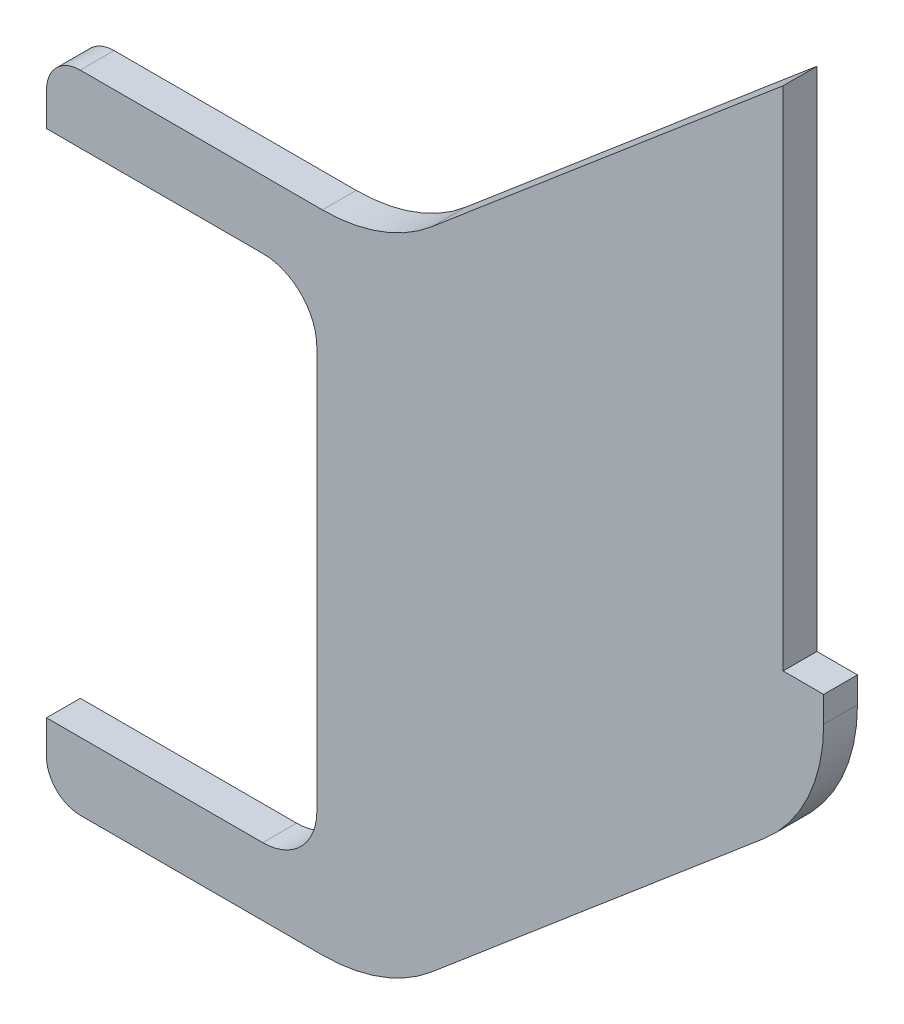
SolidWorks part; units mm, degrees
material "Acier allié"
ref_plane "Plan de face" through (0, 0, 0) normal (0, 0, 1) x (1, 0, 0)
ref_plane "Plan de dessus" through (0, 0, 0) normal (0, 1, 0) x (1, 0, 0)
ref_plane "Plan de droite" through (0, 0, 0) normal (1, 0, 0) x (0, 0, -1)
sketch "Esquisse1" plane through (0, 0, 0) normal (0, 0, 1) x (1, 0, 0)
  line L0 (80, 171) -> (0, 171)
  line L1 (0, 0) -> (100, 0)
  line L2 (0, 191) -> (100, 191)
  line L3 (100, 191) -> (218, 291)
  line L4 (0, 171) -> (0, 191)
  line L5 (80, 20) -> (0, 20)
  line L6 (80, 20) -> (80, 171)
  line L7 (0, 20) -> (0, 0)
  line L8 (230, 110.1695) -> (230, 141)
  line L9 (230, 110.1695) -> (100, 0)
  line L10 (230, 141) -> (218, 141)
  line L11 (218, 141) -> (218, 291)
  dimension "D1" = 151
  dimension "D2" = 80
  dimension "D3" = 80
  dimension "D4" = 20
  dimension "D5" = 20
  dimension "D6" = 100
  dimension "D7" = 150
  dimension "D8" = 100
  dimension "D9" = 12
  dimension "D10" = 230
extrude "Boss.-Extru.1" add sketch "Esquisse1" along normal blind 10
fillet "Congé2" radius 16 2 edges at (80, 171, 5) (80, 20, 5)
fillet "Congé3" radius 10 2 edges at (0, 0, 5) (0, 191, 5)
fillet "Congé4" radius 50 3 edges at (230, 110.1695, 5) (100, 0, 5) (100, 191, 5)
